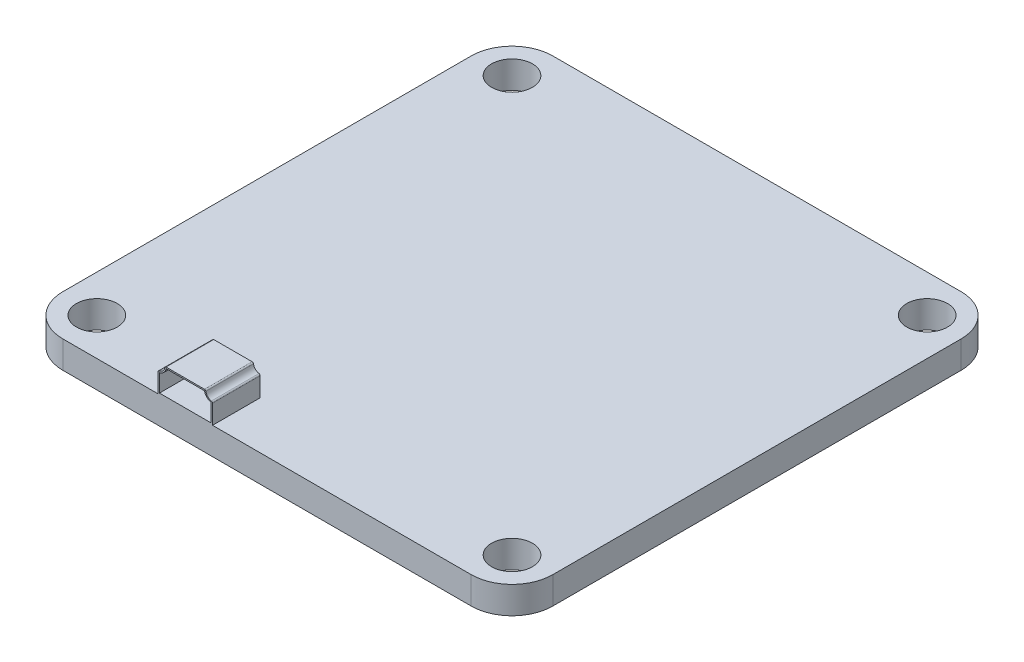
SolidWorks part; units mm, degrees
ref_plane "Front Plane" through (0, 0, 0) normal (0, 0, 1) x (1, 0, 0)
ref_plane "Top Plane" through (0, 0, 0) normal (0, 1, 0) x (1, 0, 0)
ref_plane "Right Plane" through (0, 0, 0) normal (1, 0, 0) x (0, 0, -1)
sketch "Sketch1" plane through (0, 0, 0) normal (0, 1, 0) x (1, 0, 0)
  line L0 (0, -18) -> (0, 18) construction
  line L1 (-15, -18) -> (15, -18)
  line L2 (-18, -15) -> (-18, 15)
  line L3 (-15, 18) -> (15, 18)
  line L4 (18, -15) -> (18, 15)
  line L5 (-18, 0) -> (18, 0) construction
  arc A0 (-15, -18) -> (-18, -15) centre (-15, -15) cw
  arc A1 (15, -18) -> (18, -15) centre (15, -15) ccw
  arc A2 (15, 18) -> (18, 15) centre (15, 15) cw
  arc A3 (-18, 15) -> (-15, 18) centre (-15, 15) cw
  circle A4 centre (15.25, 15.25) radius 1.5
  circle A5 centre (-15.25, 15.25) radius 1.5
  circle A6 centre (15.25, -15.25) radius 1.5
  circle A7 centre (-15.25, -15.25) radius 1.5
  point P0 (0, 0)
  point P12 (-18, -18)
  point P17 (18, 18)
  point P20 (-18, 18)
  dimension "D3" = 3
  dimension "D4" = 3
  dimension "D1" = 36
  dimension "D2" = 36
  dimension "D5" = 15.25
  dimension "D6" = 15.25
extrude "Boss-Extrude1" add sketch "Sketch1" along normal mid plane 2
sketch "Sketch2" plane through (0, 0, 18) normal (0, 0, 1) x (1, 0, 0)
  line L0 (-15, 1) -> (15, 1) construction
  line L1 (-8, 1) -> (-4, 1)
  line L2 (-8, 1) -> (-8, 2.4084)
  line L3 (-7.4084, 3) -> (-4.5916, 3)
  line L4 (-4, 1) -> (-4, 2.4084)
  line L5 (-18, 1) -> (-18, -1) construction
  line L6 (-4.1, 1.1) -> (-4.1, 2.4084)
  line L7 (-7.9, 1.1) -> (-4.1, 1.1)
  line L8 (-7.9, 1.1) -> (-7.9, 2.4084)
  line L9 (-7.4084, 2.9) -> (-4.5916, 2.9)
  arc A0 (-7.9167, 2.507) -> (-7.507, 2.9167) centre (-8, 3) ccw
  arc A1 (-4.493, 2.9167) -> (-4.0833, 2.507) centre (-4, 3) ccw
  arc A2 (-4.0833, 2.507) -> (-4, 2.4084) centre (-4.1, 2.4084) cw
  arc A3 (-4.493, 2.9167) -> (-4.5916, 3) centre (-4.5916, 2.9) ccw
  arc A4 (-7.9167, 2.507) -> (-8, 2.4084) centre (-7.9, 2.4084) ccw
  arc A5 (-7.507, 2.9167) -> (-7.4084, 3) centre (-7.4084, 2.9) cw
  arc A6 (-4.5916, 2.9) -> (-4.1, 2.4084) centre (-4, 3) ccw
  arc A7 (-4.1, 2.4084) -> (-4.1, 2.4084) centre (-4.1, 2.4084) cw
  arc A8 (-7.9, 2.4084) -> (-7.9, 2.4084) centre (-7.9, 2.4084) ccw
  arc A9 (-7.9, 2.4084) -> (-7.4084, 2.9) centre (-8, 3) ccw
  arc A10 (-7.4084, 2.9) -> (-7.4084, 2.9) centre (-7.4084, 2.9) cw
  arc A11 (-4.5916, 2.9) -> (-4.5916, 2.9) centre (-4.5916, 2.9) ccw
  dimension "D4" = 1
  dimension "D5" = 1
  dimension "D6" = 0.1
  dimension "D1" = 2
  dimension "D2" = 4
  dimension "D3" = 10
  dimension "D7" = 0.1
extrude "Boss-Extrude2" add sketch "Sketch2" against normal blind 3.5
sketch "Sketch3" plane through (0, 0, 14.5) normal (0, 0, -1) x (-1, 0, 0)
  line L4 (8, 1) -> (8, 2.4084)
  line L5 (7.4084, 3) -> (4.5916, 3)
  line L6 (4, 2.4084) -> (4, 1)
  line L7 (4, 1) -> (8, 1)
  line L8 (8, 1) -> (8, 2.4084)
  line L9 (7.4084, 3) -> (4.5916, 3)
  line L10 (4, 2.4084) -> (4, 1)
  line L11 (4, 1) -> (8, 1)
  arc A6 (8, 2.4084) -> (7.9167, 2.507) centre (7.9, 2.4084) ccw
  arc A7 (7.507, 2.9167) -> (7.9167, 2.507) centre (8, 3) ccw
  arc A8 (7.507, 2.9167) -> (7.4084, 3) centre (7.4084, 2.9) ccw
  arc A9 (4.5916, 3) -> (4.493, 2.9167) centre (4.5916, 2.9) ccw
  arc A10 (4.0833, 2.507) -> (4.493, 2.9167) centre (4, 3) ccw
  arc A11 (4.0833, 2.507) -> (4, 2.4084) centre (4.1, 2.4084) ccw
  arc A12 (8, 2.4084) -> (7.9167, 2.507) centre (7.9, 2.4084) ccw
  arc A13 (7.507, 2.9167) -> (7.9167, 2.507) centre (8, 3) ccw
  arc A14 (7.507, 2.9167) -> (7.4084, 3) centre (7.4084, 2.9) ccw
  arc A15 (4.5916, 3) -> (4.493, 2.9167) centre (4.5916, 2.9) ccw
  arc A16 (4.0833, 2.507) -> (4.493, 2.9167) centre (4, 3) ccw
  arc A17 (4.0833, 2.507) -> (4, 2.4084) centre (4.1, 2.4084) ccw
  dimension "D1" = 0
extrude "Boss-Extrude3" add sketch "Sketch3" against normal blind 0.5
sketch "Sketch4" plane through (0, 0, 15) normal (0, 0, 1) x (1, 0, 0)
  line L0 (-4.5916, 3) -> (-7.4084, 3) construction
  line L2 (-7.9, 1.1) -> (-4.1, 1.1) construction
  circle A0 centre (-7, 2.6) radius 0.25
  circle A1 centre (-6, 2.6) radius 0.25
  circle A2 centre (-5, 2.6) radius 0.25
  point P2 (0, 0)
  point P9 (-6, 3)
  point P10 (0, 0)
  dimension "D1" = 0.5
  dimension "D3" = 1.5
  dimension "D2" = 3
extrude "Cut-Extrude1" cut sketch "Sketch4" against normal through all
